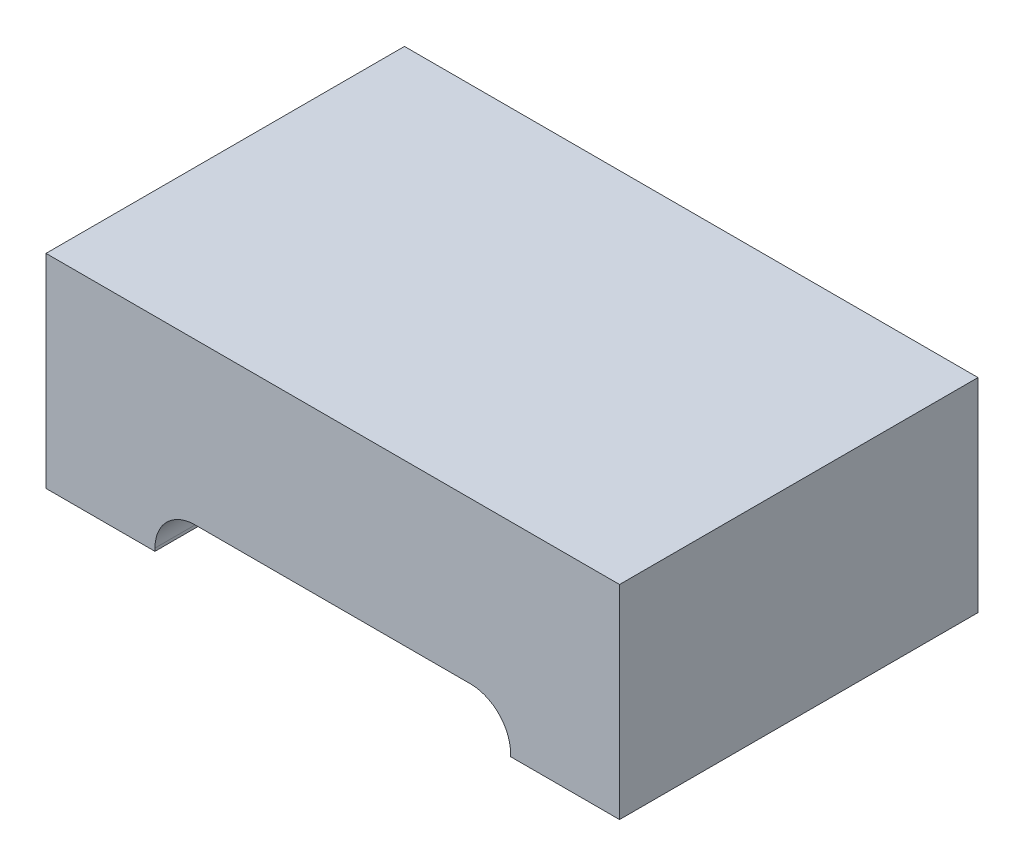
SolidWorks part; units mm, degrees
ref_plane "Front Plane" through (0, 0, 0) normal (0, 0, 1) x (1, 0, 0)
ref_plane "Top Plane" through (0, 0, 0) normal (0, 1, 0) x (1, 0, 0)
ref_plane "Right Plane" through (0, 0, 0) normal (1, 0, 0) x (0, 0, -1)
sketch "Sketch1" plane through (0, 0, 0) normal (0, 1, 0) x (1, 0, 0)
  line L1 (-1, -0.625) -> (1, -0.625)
  line L2 (-1, -0.625) -> (-1, 0.625)
  line L3 (-1, 0.625) -> (1, 0.625)
  line L4 (1, -0.625) -> (1, 0.625)
  line L5 (-1, -0.625) -> (1, 0.625) construction
  line L6 (-1, 0.625) -> (1, -0.625) construction
  point P0 (0, 0)
  dimension "D1" = 2
  dimension "D2" = 1.25
extrude "Boss-Extrude1" add sketch "Sketch1" along normal blind 0.71
sketch "Sketch2" plane through (0, 0, 0) normal (0, 0, 1) x (1, 0, 0)
  line L0 (-1, 0.71) -> (-1, 0) construction
  line L1 (-0.62, 0) -> (0.62, 0)
  line L2 (-0.62, 0) -> (-0.62, 0.01)
  line L3 (-0.48, 0.15) -> (0.48, 0.15)
  line L4 (0.62, 0) -> (0.62, 0.01)
  arc A0 (0.48, 0.15) -> (0.62, 0.01) centre (0.48, 0.01) cw
  arc A1 (-0.62, 0.01) -> (-0.48, 0.15) centre (-0.48, 0.01) cw
  point P4 (0, 0)
  point P10 (0.62, 0.15)
  dimension "D3" = 0.14
  dimension "D1" = 0.38
  dimension "D2" = 0.15
extrude "Cut-Extrude1" cut sketch "Sketch2" against normal through all both and the other way through all
